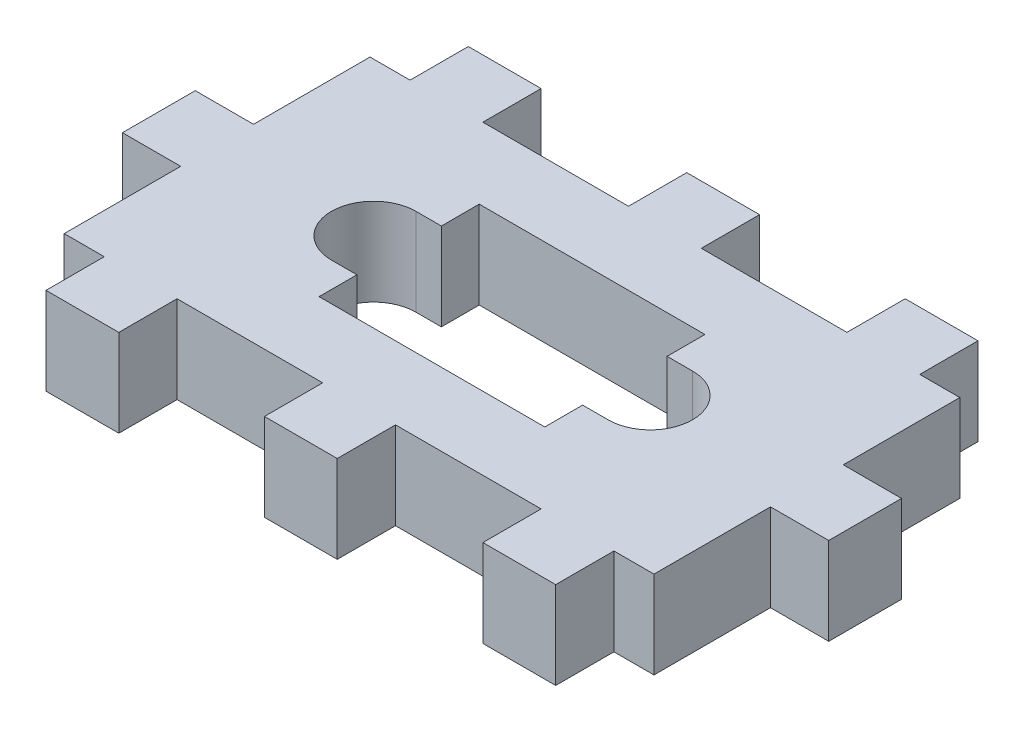
SolidWorks part; units mm, degrees
material "Maple"
ref_plane "Front Plane" through (0, 0, 0) normal (0, 0, 1) x (1, 0, 0)
ref_plane "Top Plane" through (0, 0, 0) normal (0, 1, 0) x (1, 0, 0)
ref_plane "Right Plane" through (0, 0, 0) normal (1, 0, 0) x (0, 0, -1)
sketch "Sketch1" plane through (0, 0, 0) normal (0, 1, 0) x (1, 0, 0)
  line L1 (0, 0) -> (15.5, 0)
  line L2 (0, 0) -> (0, -11)
  line L3 (0, -11) -> (15.5, -11)
  line L4 (15.5, 0) -> (15.5, -11)
  dimension "D1" = 15.5
  dimension "D2" = 11
extrude "Boss-Extrude1" add sketch "Sketch1" along normal blind 1.6
sketch "Sketch2" plane through (0, 1.6, 0) normal (0, 1, 0) x (1, 0, 0)
  line L0 (0, -5.5) -> (15.5, -5.5) construction
  line L1 (0, 0) -> (0, -11) construction
  line L2 (15.5, -11) -> (15.5, 0) construction
  line L3 (0, -5.5) -> (-1.75, -5.5) construction
  line L4 (15.5, -5.5) -> (17.25, -5.5) construction
  line L6 (-1.75, -2.6) -> (17.25, -2.6)
  line L7 (-1.75, -2.6) -> (-1.75, -8.4)
  line L8 (-1.75, -8.4) -> (17.25, -8.4)
  line L9 (17.25, -2.6) -> (17.25, -8.4)
  circle A0 centre (-1.75, -5.5) radius 1.5
  circle A1 centre (17.25, -5.5) radius 1.5
  circle A2 centre (-1.75, -5.5) radius 2.9
  circle A3 centre (17.25, -5.5) radius 2.9
  line M3 (0, 0) -> (0, -11)
  line M5 (15.5, -11) -> (15.5, 0)
  dimension "D2" = 3
  dimension "D3" = 3
  dimension "D4" = 5.8
  dimension "D5" = 5.8
  dimension "D1" = 19
extrude "Boss-Extrude2" add sketch "Sketch2" against normal through all contours L7 A2 A0 | L7 A2 A0 M3 | A2 L6 M3 | A2 L8 M3 | L9 A3 A1 | L9 A3 A1 M5 | A3 L6 M5 | A3 L8 M5
sketch "Sketch3" plane through (0, 1.6, 0) normal (0, 1, 0) x (1, 0, 0)
  line L0 (7.75, 0) -> (7.75, -11) construction
  line L2 (-12.5, 5) -> (28, 5)
  line L3 (-12.5, 5) -> (-12.5, -16)
  line L4 (-12.5, -16) -> (28, -16)
  line L5 (28, 5) -> (28, -16)
  line L6 (-12.5, 5) -> (28, -16) construction
  line L7 (-12.5, -16) -> (28, 5) construction
  line L10 (0, 0) -> (0, -2.6)
  line L11 (0, -2.6) -> (-1.75, -2.6)
  line L12 (-1.75, -8.4) -> (0, -8.4)
  line L13 (0, -8.4) -> (0, -11)
  line L14 (0, -11) -> (15.5, -11)
  line L15 (15.5, -11) -> (15.5, -8.4)
  line L16 (15.5, -8.4) -> (17.25, -8.4)
  line L17 (17.25, -2.6) -> (15.5, -2.6)
  line L18 (15.5, -2.6) -> (15.5, 0)
  line L19 (15.5, 0) -> (0, 0)
  line L20 (0, 0) -> (0, -2.6)
  line L21 (0, -2.6) -> (-1.75, -2.6)
  line L22 (-1.75, -8.4) -> (0, -8.4)
  line L23 (0, -8.4) -> (0, -11)
  line L24 (0, -11) -> (15.5, -11)
  line L25 (15.5, -11) -> (15.5, -8.4)
  line L26 (15.5, -8.4) -> (17.25, -8.4)
  line L27 (17.25, -2.6) -> (15.5, -2.6)
  line L28 (15.5, -2.6) -> (15.5, 0)
  line L29 (15.5, 0) -> (0, 0)
  arc A2 (-1.75, -2.6) -> (-1.75, -8.4) centre (-1.75, -5.5) ccw
  arc A3 (17.25, -8.4) -> (17.25, -2.6) centre (17.25, -5.5) ccw
  arc A4 (-1.75, -2.6) -> (-1.75, -8.4) centre (-1.75, -5.5) ccw
  arc A5 (17.25, -8.4) -> (17.25, -2.6) centre (17.25, -5.5) ccw
  point P9 (7.75, -5.5)
  point P18 (0, 0)
  point P20 (7.5925, -3.8728)
  point P22 (0, 0)
  dimension "D2" = 40.5
  dimension "D3" = 21
  dimension "D4" = 5
  dimension "D1" = 0
extrude "Boss-Extrude3" add sketch "Sketch3" along normal blind 6 separate body
sketch "Sketch4" plane through (0, 1.6, 0) normal (0, 1, 0) x (1, 0, 0)
  line L10 (0, 0) -> (0, -2.6)
  line L11 (0, -2.6) -> (-1.75, -2.6)
  line L12 (-1.75, -8.4) -> (0, -8.4)
  line L13 (0, -8.4) -> (0, -11)
  line L14 (0, -11) -> (15.5, -11)
  line L15 (15.5, -11) -> (15.5, -8.4)
  line L16 (15.5, -8.4) -> (17.25, -8.4)
  line L17 (17.25, -2.6) -> (15.5, -2.6)
  line L18 (15.5, -2.6) -> (15.5, 0)
  line L19 (15.5, 0) -> (0, 0)
  line L20 (0, 0) -> (0, -2.6)
  line L21 (0, -2.6) -> (-1.75, -2.6)
  line L22 (-1.75, -8.4) -> (0, -8.4)
  line L23 (0, -8.4) -> (0, -11)
  line L24 (0, -11) -> (15.5, -11)
  line L25 (15.5, -11) -> (15.5, -8.4)
  line L26 (15.5, -8.4) -> (17.25, -8.4)
  line L27 (17.25, -2.6) -> (15.5, -2.6)
  line L28 (15.5, -2.6) -> (15.5, 0)
  line L29 (15.5, 0) -> (0, 0)
  arc A2 (-1.75, -2.6) -> (-1.75, -8.4) centre (-1.75, -5.5) ccw
  arc A3 (17.25, -8.4) -> (17.25, -2.6) centre (17.25, -5.5) ccw
  arc A4 (-1.75, -2.6) -> (-1.75, -8.4) centre (-1.75, -5.5) ccw
  arc A5 (17.25, -8.4) -> (17.25, -2.6) centre (17.25, -5.5) ccw
  dimension "D1" = 0
extrude "Cut-Extrude1" cut sketch "Sketch4" against normal through all
sketch "Sketch5" plane through (0, 7.6, 0) normal (0, 1, 0) x (1, 0, 0)
  line L0 (7.75, 5) -> (7.75, -16) construction
  line L1 (28, 5) -> (-12.5, 5) construction
  line L2 (-12.5, -16) -> (28, -16) construction
  line L4 (5.25, 5) -> (10.25, 5)
  line L5 (5.25, 5) -> (5.25, 9)
  line L6 (5.25, 9) -> (10.25, 9)
  line L7 (10.25, 5) -> (10.25, 9)
  line L8 (5.25, 5) -> (10.25, 9) construction
  line L9 (5.25, 9) -> (10.25, 5) construction
  line L10 (5.25, -16) -> (10.25, -16)
  line L11 (5.25, -16) -> (5.25, -20)
  line L12 (5.25, -20) -> (10.25, -20)
  line L13 (10.25, -16) -> (10.25, -20)
  line L14 (5.25, -16) -> (10.25, -20) construction
  line L15 (5.25, -20) -> (10.25, -16) construction
  point P6 (7.75, 7)
  point P11 (7.75, -18)
  dimension "D1" = 4
  dimension "D2" = 4
  dimension "D3" = 5
  dimension "D4" = 5
extrude "Boss-Extrude4" add sketch "Sketch5" against normal through all
pattern_linear "LPattern1" count 2 spacing 15 along (1, 0, 0) count 2 spacing 15 along (-1, 0, 0) of "Boss-Extrude4"
sketch "Sketch6" plane through (0, 7.6, 0) normal (0, 1, 0) x (1, 0, 0)
  line L0 (-12.5, -5.5) -> (28, -5.5) construction
  line L1 (-12.5, 5) -> (-12.5, -16) construction
  line L2 (28, -16) -> (28, 5) construction
  line L4 (-16.5, -3) -> (-12.5, -3)
  line L5 (-16.5, -3) -> (-16.5, -8)
  line L6 (-16.5, -8) -> (-12.5, -8)
  line L7 (-12.5, -3) -> (-12.5, -8)
  line L8 (-16.5, -3) -> (-12.5, -8) construction
  line L9 (-16.5, -8) -> (-12.5, -3) construction
  line L10 (28, -3) -> (32, -3)
  line L11 (28, -3) -> (28, -8)
  line L12 (28, -8) -> (32, -8)
  line L13 (32, -3) -> (32, -8)
  line L14 (28, -3) -> (32, -8) construction
  line L15 (28, -8) -> (32, -3) construction
  point P6 (-14.5, -5.5)
  point P11 (30, -5.5)
  point P16 (33.6826, -7)
  point P17 (-17.9961, -7)
  dimension "D1" = 4
  dimension "D2" = 5
extrude "Boss-Extrude5" add sketch "Sketch6" against normal through all
equation "\"D3@Sketch2\"=\"D2@Sketch2\""
equation "\"D5@Sketch2\"=\"D4@Sketch2\""
equation "\"D2@Sketch5\"=\"D1@Sketch5\""
equation "\"D4@Sketch5\"=\"D3@Sketch5\""
